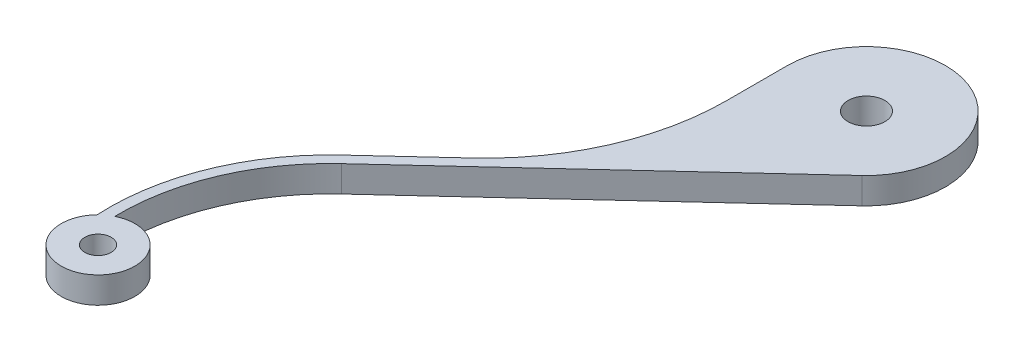
SolidWorks part; units mm, degrees
ref_plane "Face" through (0, 0, 0) normal (0, 0, 1) x (1, 0, 0)
ref_plane "Dessus" through (0, 0, 0) normal (0, 1, 0) x (1, 0, 0)
ref_plane "Droite" through (0, 0, 0) normal (1, 0, 0) x (0, 0, -1)
sketch "Esquisse1" plane through (0, 0, 0) normal (0, 1, 0) x (1, 0, 0)
  line L0 (0, 0) -> (0, -56.0148) construction
  line L1 (0, 0) -> (-33.8085, 0) construction
  line L2 (10.1805, -11.0163) -> (-41.2287, -58.5252)
  line L3 (-15, 0) -> (-15, -11.519)
  line L4 (-29.7207, -45.167) -> (-42.5861, -57.0563)
  circle A0 centre (0, 0) radius 3.5
  arc A1 (10.1805, -11.0163) -> (-15, 0) centre (0, 0) ccw
  arc A2 (-41.2287, -58.5252) -> (-54.0724, -88.7186) centre (-14.0808, -87.9018) ccw
  arc A3 (-15, -11.519) -> (-29.7207, -45.167) centre (-60.816, -11.519) cw
  arc A4 (-42.5861, -57.0563) -> (-56.0211, -90.1402) centre (-14.0808, -87.9018) ccw
  arc A5 (-54.0724, -88.7186) -> (-56.0211, -90.1402) centre (-50.983, -95) cw
  circle A6 centre (-50.983, -95) radius 2.5
  dimension "D1" = 7
  dimension "D3" = 15
  dimension "D4" = 40
  dimension "D5" = 7
  dimension "D6" = 5
  dimension "D2" = 2
  dimension "D7" = 95
  dimension "D8" = 70
extrude "Extrusion1" add sketch "Esquisse1" along normal blind 5
